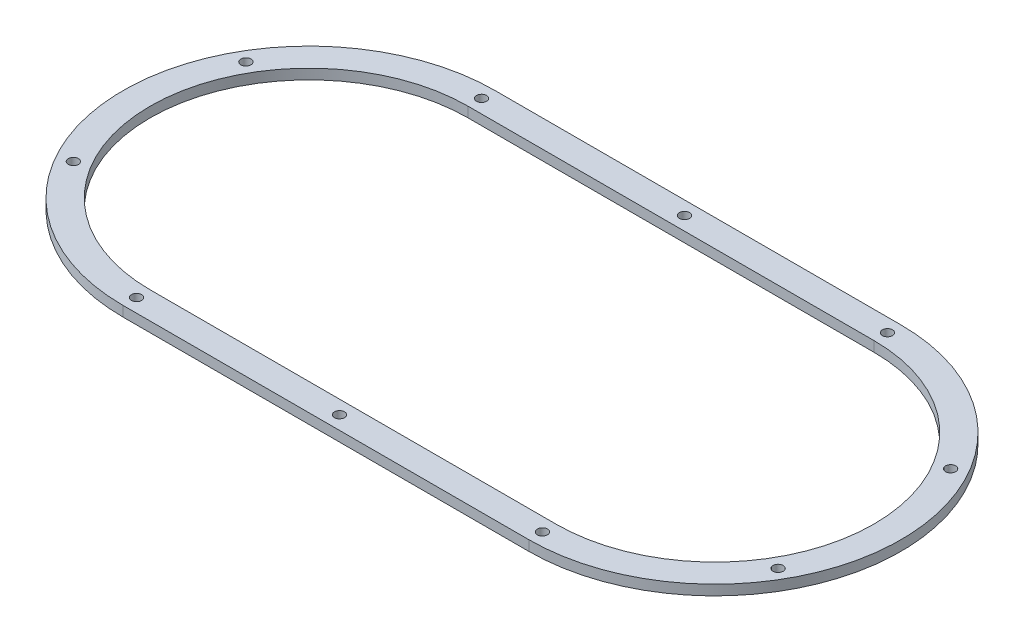
SolidWorks part; units mm, degrees
ref_plane "前视基准面" through (0, 0, 0) normal (0, 0, 1) x (1, 0, 0)
ref_plane "上视基准面" through (0, 0, 0) normal (0, 1, 0) x (1, 0, 0)
ref_plane "右视基准面" through (0, 0, 0) normal (1, 0, 0) x (0, 0, -1)
sketch "草图1" plane through (0, 0, 0) normal (0, 1, 0) x (1, 0, 0)
  line L0 (0, 0) -> (0, 89.0672) construction
  line L1 (-60, 0) -> (60, 0) construction
  line L2 (-60, 70) -> (60, 70)
  line L3 (-60, -70) -> (60, -70)
  line L4 (-90, 51.9615) -> (-60, 0) construction
  line L5 (-90, -51.9615) -> (-60, 0) construction
  line L8 (0, 0) -> (76.6344, 0) construction
  line L9 (-49.5811, 59.0885) -> (-60, 0) construction
  line L10 (-116.3816, -20.5212) -> (-60, 0) construction
  line L11 (-14.0373, -38.5673) -> (-60, 0) construction
  arc A2 (-60, 70) -> (-60, -70) centre (-60, 0) ccw
  arc A3 (60, -70) -> (60, 70) centre (60, 0) ccw
  circle A4 centre (0, 0) radius 1.5 construction
  circle A5 centre (-90, 51.9615) radius 1.5 construction
  circle A6 centre (-90, -51.9615) radius 1.5 construction
  circle A7 centre (90, -51.9615) radius 1.5 construction
  circle A8 centre (90, 51.9615) radius 1.5 construction
  circle A10 centre (-122, 0) radius 1.5
  circle A11 centre (122, 0) radius 1.5
  circle A12 centre (-30, 60) radius 1.5
  circle A13 centre (30, 60) radius 1.5
  circle A14 centre (30, -60) radius 1.5
  circle A15 centre (-30, -60) radius 1.5
  point P7 (0, 0)
  dimension "D4" = 3
  dimension "D7" = 3
  dimension "D9" = 3
  dimension "D10" = 60
  dimension "D12" = 3
  dimension "D13" = 62
  dimension "D14" = 62
  dimension "D15" = 3
  dimension "D16" = 3
  dimension "D18" = 60
  dimension "D8" = 120
  dimension "D11" = 120
  dimension "D17" = 30
  dimension "D20" = 60
  dimension "D21" = 80
  dimension "D24" = 120
  dimension "D26" = 60
  dimension "D27" = 120
extrude "凸台-拉伸2" add sketch "草图1" along normal blind 3
sketch "草图3" plane through (0, 3, 0) normal (0, 1, 0) x (1, 0, 0)
  line L2 (-60, -55) -> (60, -55)
  line L3 (60, 55) -> (-60, 55)
  line L4 (-60, -70) -> (60, -70)
  line L5 (60, 70) -> (-60, 70)
  line L6 (-60, -70) -> (60, -70)
  line L7 (60, 70) -> (-60, 70)
  arc A2 (60, -55) -> (60, 55) centre (60, 0) ccw
  arc A3 (-60, 55) -> (-60, -55) centre (-60, 0) ccw
  arc A4 (60, -70) -> (60, 70) centre (60, 0) ccw
  arc A5 (-60, 70) -> (-60, -70) centre (-60, 0) ccw
  arc A6 (60, -70) -> (60, 70) centre (60, 0) ccw
  arc A7 (-60, 70) -> (-60, -70) centre (-60, 0) ccw
  dimension "D1" = 0
  dimension "D2" = 15
extrude "切除-拉伸1" cut sketch "草图3" against normal blind 10
sketch "草图4" plane through (0, 3, 0) normal (0, 1, 0) x (1, 0, 0)
  line L2 (60, 35) -> (-60, 35) construction
  line L3 (-60, -35) -> (60, -35) construction
  line L6 (60, 55) -> (-60, 55)
  line L7 (-60, -55) -> (60, -55)
  line L8 (60, 55) -> (-60, 55) construction
  line L9 (-60, -55) -> (60, -55) construction
  line L10 (-1.65, 0) -> (1.65, 0) construction
  line L11 (0, -1.65) -> (0, 1.65) construction
  arc A2 (-60, 35) -> (-60, -35) centre (-60, 0) ccw construction
  arc A3 (60, -35) -> (60, 35) centre (60, 0) ccw construction
  arc A22 (-60, 55) -> (-60, -55) centre (-60, 0) ccw
  arc A23 (60, -55) -> (60, 55) centre (60, 0) ccw
  arc A24 (-60, 55) -> (-60, -55) centre (-60, 0) ccw construction
  arc A25 (60, -55) -> (60, 55) centre (60, 0) ccw construction
  circle A26 centre (-60, 35) radius 5
  circle A31 centre (-60, -35) radius 5
  circle A32 centre (-80.5725, -28.3156) radius 5
  circle A33 centre (-93.287, -10.8156) radius 5
  circle A34 centre (-93.287, 10.8156) radius 5
  circle A35 centre (-80.5725, 28.3156) radius 5
  circle A36 centre (-39.4275, 28.3156) radius 5 [skipped]
  circle A37 centre (-26.713, 10.8156) radius 5 [skipped]
  circle A38 centre (-26.713, -10.8156) radius 5 [skipped]
  circle A39 centre (-39.4275, -28.3156) radius 5 [skipped]
  circle A40 centre (-40, 35) radius 5
  circle A41 centre (-20, 35) radius 5
  circle A42 centre (0, 35) radius 5
  circle A43 centre (20, 35) radius 5
  circle A44 centre (40, 35) radius 5
  circle A45 centre (60, 35) radius 5
  circle A46 centre (60, -35) radius 5
  circle A47 centre (40, -35) radius 5
  circle A48 centre (20, -35) radius 5
  circle A49 centre (0, -35) radius 5
  circle A50 centre (-20, -35) radius 5
  circle A51 centre (-40, -35) radius 5
  circle A52 centre (80.5725, 28.3156) radius 5
  circle A53 centre (93.287, 10.8156) radius 5
  circle A54 centre (93.287, -10.8156) radius 5
  circle A55 centre (80.5725, -28.3156) radius 5
  point P34 (-60, 0)
  dimension "D3" = 10
  dimension "D4" = 10
  dimension "D5" = 7
  dimension "D2" = 20
  dimension "D1" = 0
extrude "切除-拉伸2" cut sketch "草图4" against normal blind 10
sketch "草图5" plane through (0, 3, 0) normal (0, 1, 0) x (1, 0, 0)
  line L0 (-60, -47) -> (60, -47) construction
  line L1 (60, 47) -> (-60, 47) construction
  line L2 (60, 55) -> (-60, 55)
  line L3 (-60, -55) -> (60, -55)
  line L5 (-60, -55) -> (60, -55) construction
  line L6 (60, 55) -> (-60, 55) construction
  line L7 (-1.65, 0) -> (1.65, 0) construction
  line L8 (0, -1.65) -> (0, 1.65) construction
  arc A0 (-60, 47) -> (-60, -47) centre (-60, 0) ccw construction
  arc A1 (60, -47) -> (60, 47) centre (60, 0) ccw construction
  arc A2 (-60, 55) -> (-60, -55) centre (-60, 0) ccw
  arc A3 (60, -55) -> (60, 55) centre (60, 0) ccw
  arc A4 (-60, 55) -> (-60, -55) centre (-60, 0) ccw construction
  arc A5 (60, -55) -> (60, 55) centre (60, 0) ccw construction
  circle A6 centre (-60, 51) radius 1.5
  circle A7 centre (0, 51) radius 1.5
  circle A8 centre (60, 51) radius 1.5
  circle A11 centre (-60, -51) radius 1.5
  circle A12 centre (-104.1673, -25.5) radius 1.5
  circle A13 centre (-104.1673, 25.5) radius 1.5
  circle A14 centre (-15.8327, -25.5) radius 1.5 [skipped]
  circle A15 centre (-15.8327, 25.5) radius 1.5 [skipped]
  circle A16 centre (60, -51) radius 1.5
  circle A17 centre (0, -51) radius 1.5
  circle A18 centre (-60, -51) radius 1.5
  circle A19 centre (104.1673, -25.5) radius 1.5
  circle A20 centre (104.1673, 25.5) radius 1.5
  point P30 (-60, 0)
  point P42 (0, 0)
  point P43 (0, 0)
  dimension "D3" = 3
  dimension "D4" = 4
  dimension "D1" = 0
  dimension "D2" = 8
  dimension "D5" = 3
  dimension "D6" = 6
extrude "切除-拉伸3" cut sketch "草图5" against normal blind 10 contours A8 | A20 | A19 | A16 | A17 | A11 | A12 | A13 | A6 | A7
sketch "草图6" plane through (0, 3, 0) normal (0, 1, 0) x (1, 0, 0)
  line L0 (60, 47) -> (-60, 47)
  line L1 (-60, -47) -> (60, -47)
  arc A0 (-60, 47) -> (-60, -47) centre (-60, 0) ccw
  arc A1 (60, -47) -> (60, 47) centre (60, 0) ccw
extrude "切除-拉伸4" cut sketch "草图6" against normal blind 10
